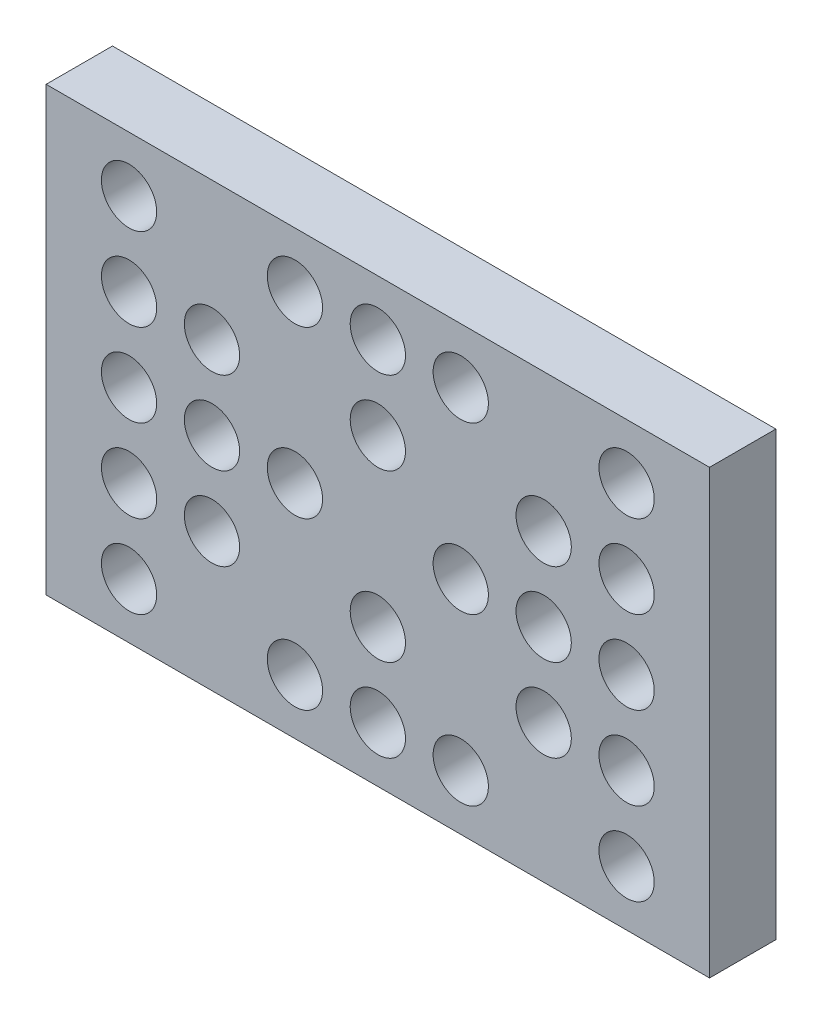
SolidWorks part; units mm, degrees
ref_plane "Přední rovina" through (0, 0, 0) normal (0, 0, 1) x (1, 0, 0)
ref_plane "Vrchní rovina" through (0, 0, 0) normal (0, 1, 0) x (1, 0, 0)
ref_plane "Pravá rovina" through (0, 0, 0) normal (1, 0, 0) x (0, 0, -1)
sketch "Skica1" plane through (0, 0, 0) normal (0, 0, 1) x (1, 0, 0)
  line L1 (-60, 40) -> (60, 40)
  line L2 (-60, 40) -> (-60, -40)
  line L3 (-60, -40) -> (60, -40)
  line L4 (60, 40) -> (60, -40)
  line L5 (-60, 40) -> (60, -40) construction
  line L6 (-60, -40) -> (60, 40) construction
  point P0 (0, 0)
  dimension "D1" = 120
  dimension "D2" = 80
extrude "Přidat vysunutím1" add sketch "Skica1" along normal blind 12
sketch "Skica2" plane through (0, 0, 0) normal (0, 0, -1) x (-1, 0, 0)
  line L0 (60, -40) -> (-60, -40) construction
  line L1 (-60, -40) -> (-60, 40) construction
  circle A0 centre (-45, -30) radius 5
  dimension "D1" = 10
  dimension "D3" = 10
  dimension "D2" = 15
extrude "Odebrat vysunutím1" cut sketch "Skica2" against normal up to next (12 mm away)
pattern_linear "LinPole1" count 7 spacing 15 along (-1, 0, 0) count 5 spacing 15 along (0, 1, 0) skipping (1, 0), (1, 4), (2, 1), (2, 3), (3, 2), (4, 1), (4, 3), (5, 0), (5, 4) of "Odebrat vysunutím1"
